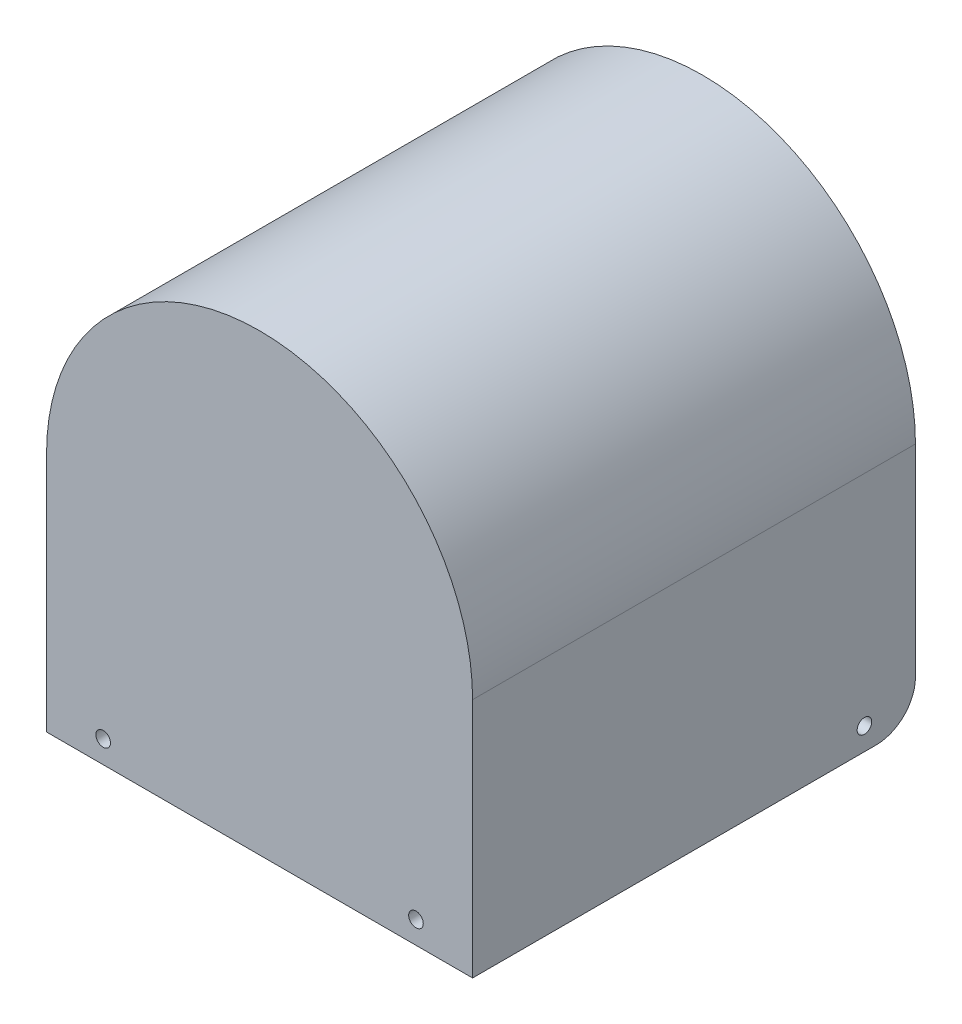
SolidWorks part; units mm, degrees
ref_plane "Front Plane" through (0, 0, 0) normal (0, 0, 1) x (1, 0, 0)
ref_plane "Top Plane" through (0, 0, 0) normal (0, 1, 0) x (1, 0, 0)
ref_plane "Right Plane" through (0, 0, 0) normal (1, 0, 0) x (0, 0, -1)
sketch "Sketch1" plane through (0, 0, 0) normal (0, 0, 1) x (1, 0, 0)
  line L0 (-36, 0) -> (-36, -43)
  line L1 (36, 0) -> (36, -43)
  line L2 (38, 0) -> (38, -43)
  line L3 (-38, 0) -> (-38, -43)
  line L4 (-38, -43) -> (-36, -43)
  line L5 (36, -43) -> (38, -43)
  arc A0 (-36, 0) -> (36, 0) centre (0, 0) cw
  arc A1 (-38, 0) -> (38, 0) centre (0, 0) cw
  dimension "D1" = 36
  dimension "D2" = 43
  dimension "D3" = 2
extrude "Boss-Extrude1" add sketch "Sketch1" along normal blind 79
sketch "Sketch2" plane through (0, 0, 0) normal (0, 1, 0) x (1, 0, 0)
  line L0 (-36, -79) -> (36, -79) construction
  line L1 (-36, -79) -> (36, -79)
  line L2 (-36, -79) -> (-36, -77)
  line L3 (-36, -77) -> (36, -77)
  line L4 (36, -79) -> (36, 0) construction
  line L5 (36, -77) -> (36, -79)
  dimension "D1" = 2
extrude "Boss-Extrude2" add sketch "Sketch2" against normal up to surface (43 mm away) and the other way up to surface up to face at (37, -43, 39.5) other way up to face at (0, 18, 39.5)
sketch "Sketch3" plane through (0, 0, 79) normal (0, 0, 1) x (1, 0, 0)
  line L0 (-38, -39) -> (38, -39) construction
  line L1 (-38, 0) -> (-38, -43) construction
  line L2 (38, -43) -> (38, 0) construction
  line L3 (-38, -43) -> (38, -43) construction
  line L4 (0, -39) -> (0, -43) construction
  circle A0 centre (-27.9, -39) radius 1.3
  circle A1 centre (27.9, -39) radius 1.3
  dimension "D3" = 2.6
  dimension "D1" = 4
  dimension "D2" = 55.8
extrude "Cut-Extrude1" cut sketch "Sketch3" against normal blind 10
sketch "Sketch4" plane through (38, 0, 0) normal (1, 0, 0) x (0, 0, -1)
  line L0 (-9.1, -43) -> (-9.1, 0) construction
  line L1 (-79, -43) -> (0, -43) construction
  line L2 (-79, 0) -> (0, 0) construction
  line L3 (0, -43) -> (0, 0) construction
  circle A0 centre (-9.1, -39) radius 1.3
  dimension "D2" = 2.6
  dimension "D1" = 9.1
  dimension "D3" = 4
extrude "Cut-Extrude2" cut sketch "Sketch4" against normal through all
fillet "Fillet1" radius 7 2 edges at (-37, -43, 0) (37, -43, 0)
